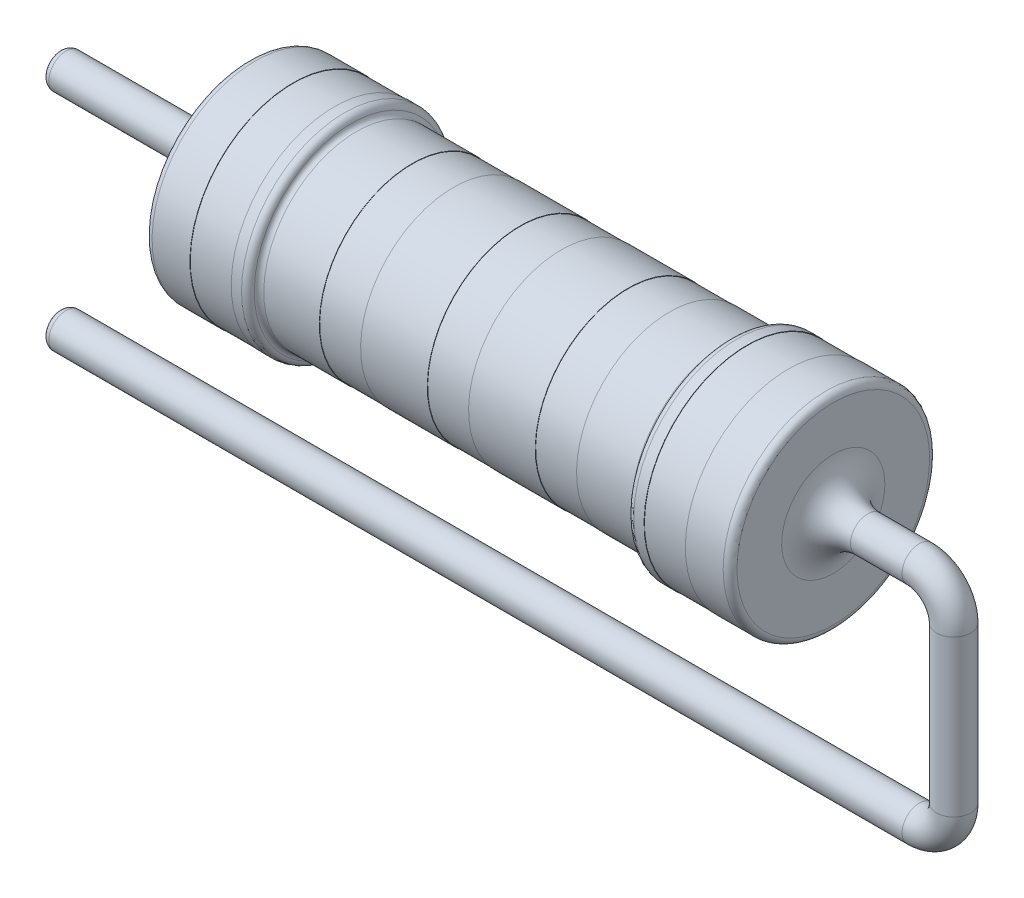
SolidWorks part; units mm, degrees
ref_plane "Front Plane" through (0, 0, 0) normal (0, 0, 1) x (1, 0, 0)
ref_plane "Top Plane" through (0, 0, 0) normal (0, 1, 0) x (1, 0, 0)
ref_plane "Right Plane" through (0, 0, 0) normal (1, 0, 0) x (0, 0, -1)
sketch "Sketch1" plane through (0, 0, 0) normal (0, 0, 1) x (1, 0, 0)
  line L0 (-8.5, 0) -> (8.5, 0)
  line L1 (8.5, 0) -> (8.5, -3)
  line L2 (8.5, -3) -> (7.2, -3)
  line L3 (7.2, -3) -> (7.2, -2.99)
  line L4 (7.2, -2.99) -> (6, -2.99)
  line L5 (6, -2.99) -> (6, -3)
  line L6 (6, -3) -> (5.5, -3)
  line L7 (5.5, -3) -> (5.5, -2.7)
  line L8 (5.5, -2.7) -> (3.738, -2.7)
  line L9 (3.738, -2.7) -> (3.738, -2.69)
  line L10 (3.738, -2.69) -> (2.538, -2.69)
  line L11 (2.538, -2.69) -> (2.538, -2.7)
  line L12 (2.538, -2.7) -> (0.6, -2.7)
  line L13 (0.6, -2.7) -> (0.6, -2.69)
  line L14 (0.6, -2.69) -> (-0.6, -2.69)
  line L16 (-0.6, -2.7) -> (-0.6, -2.69)
  line L17 (-2.538, -2.7) -> (-0.6, -2.7)
  line L18 (-2.538, -2.69) -> (-2.538, -2.7)
  line L19 (-3.738, -2.69) -> (-2.538, -2.69)
  line L20 (-3.738, -2.7) -> (-3.738, -2.69)
  line L21 (-5.5, -2.7) -> (-3.738, -2.7)
  line L22 (-5.5, -3) -> (-5.5, -2.7)
  line L23 (-6, -3) -> (-5.5, -3)
  line L24 (-6, -2.99) -> (-6, -3)
  line L25 (-7.2, -2.99) -> (-6, -2.99)
  line L26 (-7.2, -3) -> (-7.2, -2.99)
  line L27 (-8.5, -3) -> (-7.2, -3)
  line L28 (-8.5, 0) -> (-8.5, -3)
  dimension "D2" = 3
  dimension "D3" = 3
  dimension "D4" = 1.3
  dimension "D5" = 1.2
  dimension "D6" = 0.01
  dimension "D7" = 0.3
  dimension "D8" = 1.2
  dimension "D9" = 0.01
  dimension "D10" = 0.01
revolve "Revolve1" add sketch "Sketch1" angle 360 about L0
sketch "Sketch2" plane through (8.5, 0, 0) normal (1, 0, 0) x (0, 0, -1)
  circle A0 centre (0, 0) radius 0.5
sketch3d "3DSketch1"
  line L0 (8.5, 0, 0) -> (11, 0, 0)
  line L1 (12, -1, 0) -> (12, -5.53, 0)
  line L2 (11, -6.53, 0) -> (-14, -6.53, 0)
  arc A0 (12, -1, 0) -> (11, 0, 0) centre (11, -1, 0) ccw
  arc A1 (11, -6.53, 0) -> (12, -5.53, 0) centre (11, -5.53, 0) ccw
  point P6 (12, 0, 0)
  point P8 (11, -1, 1)
  point P12 (12, -6.53, 0)
  point P13 (11, -5.53, 1)
  dimension "D2" = 1
  dimension "D4" = 1
  dimension "D1" = 3.5
  dimension "D3" = 26
fillet "Fillet1" radius 0.2 4 edges at (5.5, -3, 0) (8.5, -3, 0) (-5.5, -3, 0) (-8.5, -3, 0)
fillet "Fillet2" radius 0.15 2 edges at (-5.5, -2.7, 0) (5.5, -2.7, 0)
sweep "Sweep1" add profiles "Sketch2" path "3DSketch1"
sketch "Sketch3" plane through (-8.5, 0, 0) normal (-1, 0, 0) x (0, 0, 1)
  circle A0 centre (0, 0) radius 0.5
sketch3d "3DSketch5"
  line L0 (-8.5, 0, 0) -> (-14, 0, 0)
  dimension "D1" = 5.5
sweep "Sweep2" add profiles "Sketch3" path "3DSketch5"
fillet "Fillet7" radius 0.2 2 edges at (-14, -7.03, 0) (-14, -0.5, 0)
fillet "Fillet8" radius 1 2 edges at (8.5, 0.5, 0) (-8.5, -0.5, 0)
